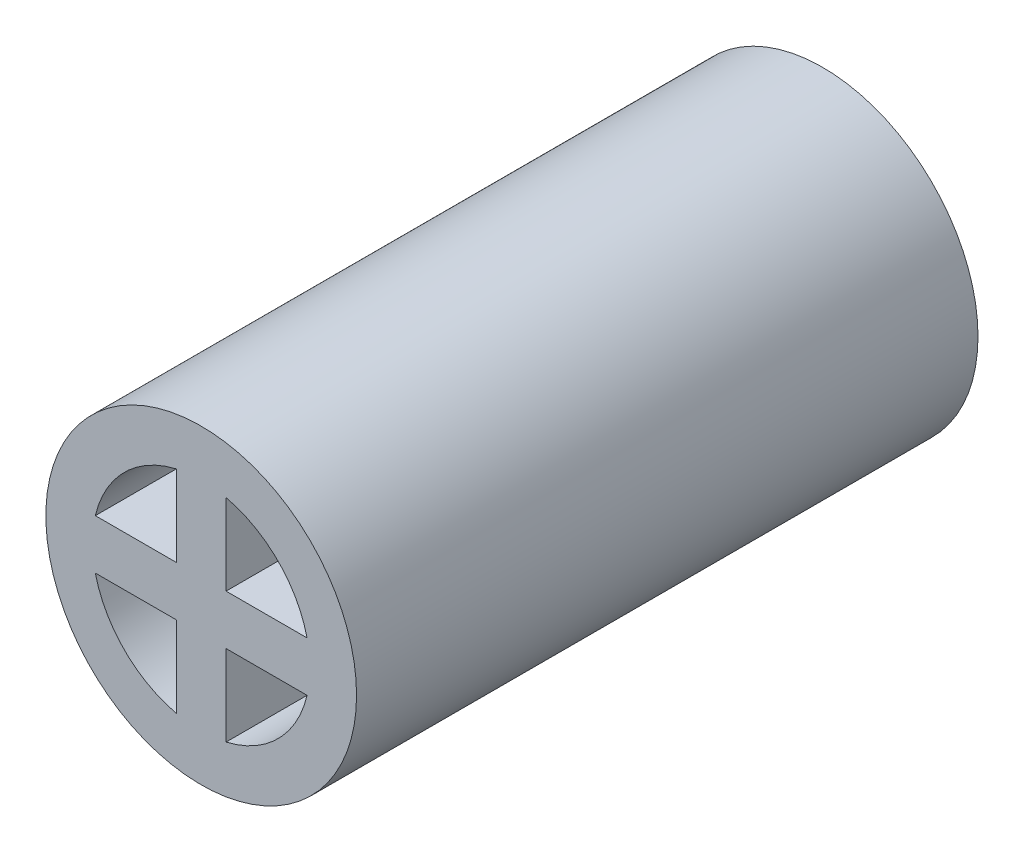
SolidWorks part; units mm, degrees
ref_plane "Front Plane" through (0, 0, 0) normal (0, 0, 1) x (1, 0, 0)
ref_plane "Top Plane" through (0, 0, 0) normal (0, 1, 0) x (1, 0, 0)
ref_plane "Right Plane" through (0, 0, 0) normal (1, 0, 0) x (0, 0, -1)
sketch "Sketch1" plane through (0, 0, 0) normal (0, 0, 1) x (1, 0, 0)
  circle A0 centre (0, 0) radius 12.5
  circle A1 centre (0, 0) radius 8.75
  dimension "D1" = 25
  dimension "D2" = 17.5
extrude "Boss-Extrude1" add sketch "Sketch1" along normal blind 50
sketch "Sketch2" plane through (0, 0, 0) normal (0, 0, 1) x (1, 0, 0)
  line L0 (0, 0) -> (-2, 0) construction
  line L1 (-2, -8.5184) -> (-2, -2)
  line L2 (0, 0) -> (0, 2) construction
  line L3 (2, -8.5184) -> (2, -2)
  line L4 (8.5184, 2) -> (2, 2)
  line L5 (8.5184, -2) -> (2, -2)
  line L6 (-2, 2) -> (-8.5184, 2)
  line L7 (2, 2) -> (2, 8.5184)
  line L8 (-2, -2) -> (-8.5184, -2)
  line L9 (-2, 2) -> (-2, 8.5184)
  arc A0 (-8.5184, 2) -> (-8.5184, -2) centre (0, 0) ccw
  arc A1 (2, 8.5184) -> (-2, 8.5184) centre (0, 0) ccw
  arc A2 (8.5184, -2) -> (8.5184, 2) centre (0, 0) ccw
  arc A3 (-2, -8.5184) -> (2, -8.5184) centre (0, 0) ccw
  point P14 (0, -2)
  dimension "D1" = 17.5
  dimension "D2" = 2
extrude "Boss-Extrude2" add sketch "Sketch2" along normal up to surface (50 mm away) up to face at (12.5, 0, 50)
